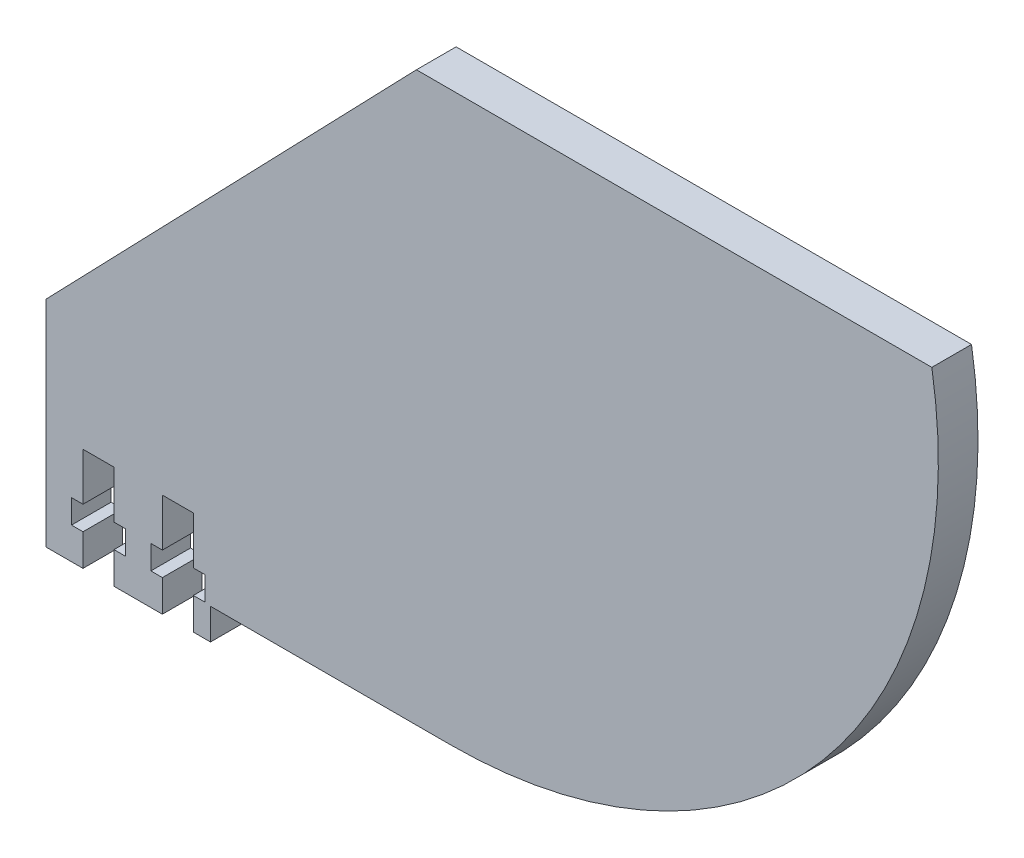
SolidWorks part; units mm, degrees
ref_plane "Front Plane" through (0, 0, 0) normal (0, 0, 1) x (1, 0, 0)
ref_plane "Top Plane" through (0, 0, 0) normal (0, 1, 0) x (1, 0, 0)
ref_plane "Right Plane" through (0, 0, 0) normal (1, 0, 0) x (0, 0, -1)
sketch "Sketch2" plane through (0, 0, 0) normal (0, 0, 1) x (1, 0, 0)
  line L0 (-252.87, -75.4) -> (-232.15, -75.4)
  line L1 (-232.15, -75.4) -> (-232.15, -71.5)
  line L2 (-252.87, -75.4) -> (-252.87, -48.3571)
  line L3 (-206.2089, 0) -> (-141.2803, 0)
  line L4 (-232.15, -71.5) -> (-201.9618, -71.5)
  line L5 (-249.87, -75.4) -> (-228.37, -75.4) construction
  line L6 (-201.9618, -72.5) -> (-224.06, -72.5) construction
  line L8 (-139.4618, 0) -> (-110.5382, 0) construction
  line L9 (-206.2089, 0) -> (-252.87, -48.3571)
  line L11 (-231.65, -70.4) -> (-231.65, -75.4) construction
  arc A0 (-201.9618, -71.5) -> (-141.2803, 0) centre (-201.9618, -10) ccw
  arc A1 (-201.9618, -72.5) -> (-139.4618, -10) centre (-201.9618, -10) ccw construction
  dimension "D1" = 1
  dimension "D2" = 0.5
extrude "Boss-Extrude1" add sketch "Sketch2" along normal blind 5
sketch "Sketch3" plane through (0, 0, 5) normal (0, 0, 1) x (1, 0, 0)
  line L0 (-248.21, -75.4) -> (-244.31, -75.4)
  line L1 (-248.21, -75.4) -> (-248.21, -71.4)
  line L2 (-246.26, -75.4) -> (-246.26, -62.4) construction
  line L3 (-248.21, -62.4) -> (-244.31, -62.4)
  line L4 (-248.21, -68.4) -> (-249.66, -68.4)
  line L5 (-249.66, -68.4) -> (-249.66, -71.4)
  line L6 (-248.21, -71.4) -> (-249.66, -71.4)
  line L7 (-248.21, -68.4) -> (-248.21, -62.4)
  line L8 (-244.31, -68.4) -> (-244.31, -62.4)
  line L9 (-244.31, -71.4) -> (-242.86, -71.4)
  line L10 (-242.86, -68.4) -> (-242.86, -71.4)
  line L11 (-244.31, -68.4) -> (-242.86, -68.4)
  line L12 (-244.31, -75.4) -> (-244.31, -71.4)
  line L13 (-244.31, -75.4) -> (-248.21, -75.4) construction
  line L14 (-252.87, -48.3571) -> (-252.87, -75.4) construction
  line L15 (-238.21, -75.4) -> (-234.31, -75.4)
  line L16 (-238.21, -75.4) -> (-238.21, -71.4)
  line L17 (-236.26, -75.4) -> (-236.26, -62.4) construction
  line L18 (-238.21, -62.4) -> (-234.31, -62.4)
  line L19 (-238.21, -68.4) -> (-239.66, -68.4)
  line L20 (-239.66, -68.4) -> (-239.66, -71.4)
  line L21 (-238.21, -71.4) -> (-239.66, -71.4)
  line L22 (-238.21, -68.4) -> (-238.21, -62.4)
  line L23 (-234.31, -68.4) -> (-234.31, -62.4)
  line L24 (-234.31, -71.4) -> (-232.86, -71.4)
  line L25 (-232.86, -68.4) -> (-232.86, -71.4)
  line L26 (-234.31, -68.4) -> (-232.86, -68.4)
  line L27 (-234.31, -75.4) -> (-234.31, -71.4)
  line L28 (-234.31, -75.4) -> (-238.21, -75.4) construction
  dimension "D1" = 3.9
  dimension "D2" = 4
  dimension "D3" = 6
  dimension "D4" = 3
  dimension "D5" = 1.45
  dimension "D6" = 3.9
  dimension "D7" = 4
  dimension "D8" = 6
  dimension "D9" = 3
  dimension "D10" = 1.45
extrude "Cut-Extrude1" cut sketch "Sketch3" against normal blind 5
